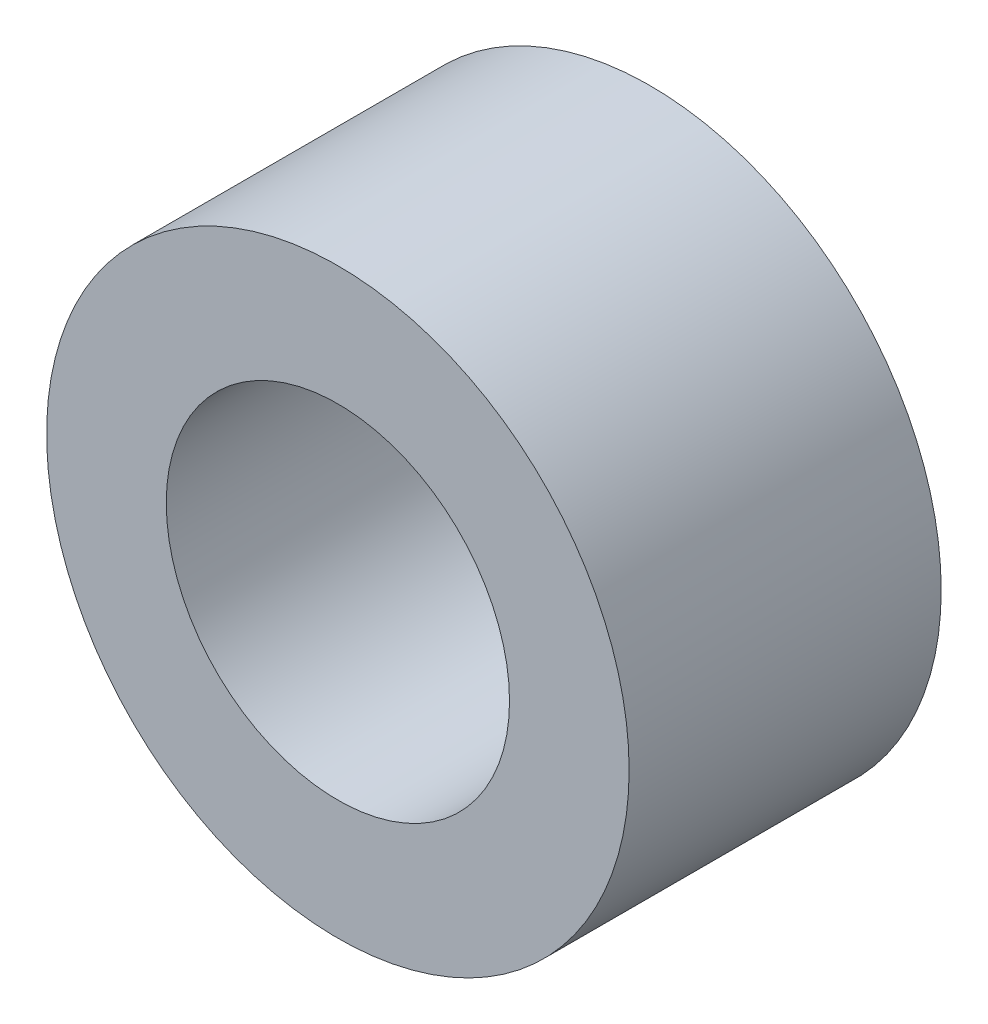
SolidWorks part; units mm, degrees
ref_plane "前视基准面" through (0, 0, 0) normal (0, 0, 1) x (1, 0, 0)
ref_plane "上视基准面" through (0, 0, 0) normal (0, 1, 0) x (1, 0, 0)
ref_plane "右视基准面" through (0, 0, 0) normal (1, 0, 0) x (0, 0, -1)
sketch "草图1" plane through (0, 0, 0) normal (0, 0, 1) x (1, 0, 0)
  circle A0 centre (0, 0) radius 1.65
  circle A1 centre (0, 0) radius 2.8
extrude "凸台-拉伸1" add sketch "草图1" along normal blind 3
